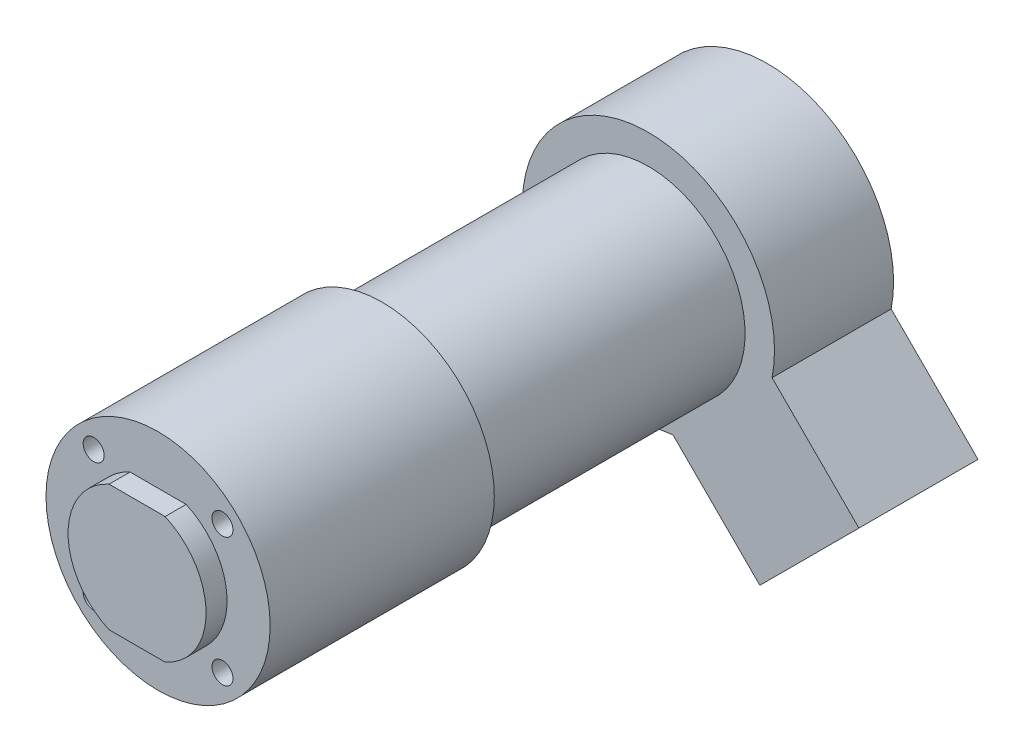
SolidWorks part; units mm, degrees
ref_plane "Front Plane" through (0, 0, 0) normal (0, 0, 1) x (1, 0, 0)
ref_plane "Top Plane" through (0, 0, 0) normal (0, 1, 0) x (1, 0, 0)
ref_plane "Right Plane" through (0, 0, 0) normal (1, 0, 0) x (0, 0, -1)
sketch "Sketch1" plane through (0, 0, 0) normal (0, 0, 1) x (1, 0, 0)
  line L0 (0, 0) -> (0, 9) construction
  line L1 (-4.0028, 9) -> (4.0028, 9)
  line L2 (-9.85, 0) -> (9.85, 0) construction
  line L3 (-4.0028, -9) -> (4.0028, -9)
  arc A0 (-4.0028, 9) -> (-4.0028, -9) centre (0, 0) ccw
  arc A1 (4.0028, -9) -> (4.0028, 9) centre (0, 0) ccw
  point P7 (0, 9)
  point P10 (0, 0)
  dimension "D1" = 19.7
  dimension "D2" = 9
extrude "Boss-Extrude1" add sketch "Sketch1" along normal blind 3
sketch "Sketch2" plane through (0, 0, 0) normal (0, 0, -1) x (-1, 0, 0)
  circle A0 centre (0, 0) radius 16
  dimension "D1" = 32
extrude "Boss-Extrude2" add sketch "Sketch2" along normal blind 32
sketch "Sketch3" plane through (0, 0, -32) normal (0, 0, -1) x (-1, 0, 0)
  circle A0 centre (0, 0) radius 13.8
  dimension "D1" = 27.6
extrude "Boss-Extrude3" add sketch "Sketch3" along normal blind 38
sketch "Sketch4" plane through (0, 0, -70) normal (0, 0, -1) x (-1, 0, 0)
  line L0 (0, 0) -> (0, -18) construction
  line L1 (0, 0) -> (-22.981, -22.981) construction
  line L2 (-30.052, -15.9099) -> (-15.9099, -30.052)
  line L3 (-30.052, -15.9099) -> (-17.6541, -3.5119)
  line L4 (-15.9099, -30.052) -> (-3.5119, -17.6541)
  circle A0 centre (0, 0) radius 18
  point P7 (-22.981, -22.981)
  circle M5 centre (0, 0) radius 13.8
  dimension "D1" = 36
  dimension "D2" = 45
  dimension "D3" = 32.5
  dimension "D4" = 20
extrude "Boss-Extrude4" add sketch "Sketch4" along normal blind 17 contours A0 M5 | M5 | A0 L3 L2 L4
sketch "Sketch5" plane through (0, 0, 3) normal (0, 0, 1) x (1, 0, 0)
  circle A0 centre (0, 0) radius 3
  dimension "D1" = 6
sketch "Sketch6" plane through (0, 0, 0) normal (0, 0, 1) x (1, 0, 0)
  line L0 (-13, 0) -> (13, 0) construction
  line L1 (0, 0) -> (-9.1924, 9.1924) construction
  circle A0 centre (0, 0) radius 13 construction
  circle A1 centre (-9.1924, 9.1924) radius 1.5
  circle A2 centre (9.1924, 9.1924) radius 1.5
  circle A3 centre (9.1924, -9.1924) radius 1.5
  circle A4 centre (-9.1924, -9.1924) radius 1.5
  point P16 (0, 0)
  dimension "D1" = 26
  dimension "D3" = 3
  dimension "D2" = 45
  dimension "D4" = 4
extrude "Cut-Extrude1" cut sketch "Sketch6" against normal blind 10 contours A2 | A1 | A4 | A3
